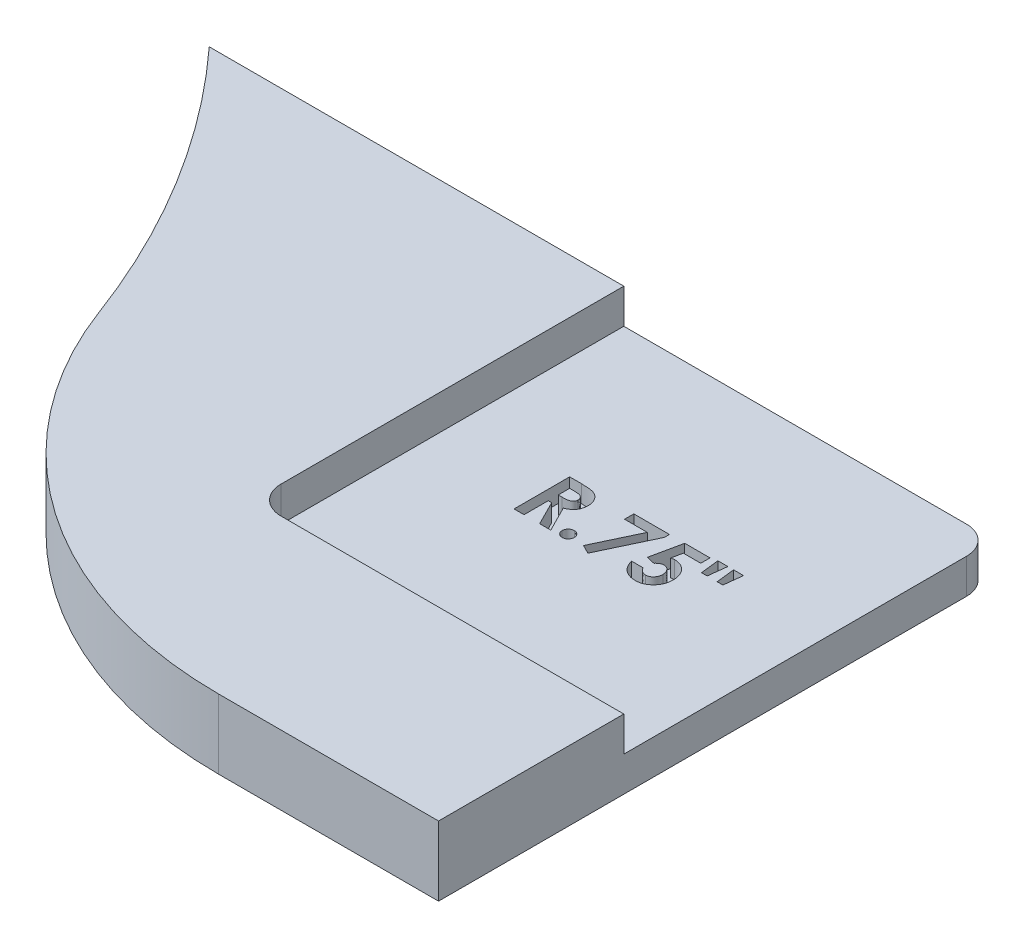
SolidWorks part; units mm, degrees
ref_plane "Front Plane" through (0, 0, 0) normal (0, 0, 1) x (1, 0, 0)
ref_plane "Top Plane" through (0, 0, 0) normal (0, 1, 0) x (1, 0, 0)
ref_plane "Right Plane" through (0, 0, 0) normal (1, 0, 0) x (0, 0, -1)
sketch "Sketch2" plane through (0, 0, 0) normal (0, 1, 0) x (1, 0, 0)
  line L0 (39.9034, 0) -> (66.5271, 0) construction
  line L4 (39.8718, 1.5875) -> (65.2718, 1.5875)
  line L5 (65.2718, 1.5875) -> (65.2718, 26.9875)
  line L6 (65.2718, 26.9875) -> (29.3931, 26.9875)
  arc A0 (39.8718, 1.5875) -> (29.3931, 26.9875) centre (0, 0) ccw
  arc A1 (29.3931, 26.9875) -> (-39.9034, 0) centre (0, 0) ccw construction
  arc A2 (-39.9034, 0) -> (39.9034, 0) centre (0, 0) ccw construction
  arc A3 (39.9034, 0) -> (39.8718, 1.5875) centre (0, 0) ccw construction
  point P6 (45.8249, 5.2638)
  point P7 (37.9479, 12.3384)
  point P10 (43.0639, 5.8161)
extrude "Boss-Extrude1" add sketch "Sketch2" along normal mid plane 3.175
fillet "Fillet1" radius 19.05 1 edges at (39.8718, 0, -1.5875)
sketch "Sketch3" plane through (0, 1.5875, 0) normal (0, 1, 0) x (1, 0, 0)
  line L1 (65.2718, 26.9875) -> (48.3385, 26.9875)
  line L2 (65.2718, 26.9875) -> (65.2718, 10.0542)
  line L3 (65.2718, 10.0542) -> (48.3385, 10.0542)
  line L4 (48.3385, 26.9875) -> (48.3385, 10.0542)
  dimension "D1" = 16.9333
extrude "Cut-Extrude1" cut sketch "Sketch3" against normal blind 1.5875
sketch "Sketch4" plane through (0, 0, 0) normal (0, 1, 0) x (1, 0, 0)
  line L0 (48.3385, 18.5208) -> (65.2718, 18.5208) construction
  line L1 (48.3385, 26.9875) -> (48.3385, 10.0542) construction
  line L2 (65.2718, 10.0542) -> (65.2718, 26.9875) construction
  line L3 (48.3385, 17.2508) -> (65.2718, 17.2508) construction
  text T0 "<b>R.75\"</b>\r\n<b> </b>" font "Century Gothic" height 2.54
  dimension "D1" = 1.27
extrude "Cut-Extrude2" cut sketch "Sketch4" against normal blind 0.7937
fillet "Fillet2" radius 1.27 2 edges at (48.3385, 0.7937, -10.0542) (65.2718, -0.7937, -26.9875)
equation "\"AIRFRAME_OD\"= 3.142in"
equation "\"AIRFRAME_ID\"= 3.00in"
equation "\"FLAT_T\"= 0.125in"
equation "\"NOSE_EXP_L\"= 3.5in"
equation "\"NOSE_SHOULDER_L\"= 5in"
equation "\"MAIN_L\"= 30in"
equation "\"RECO_COUP_L\"= 6in"
equation "\"RECO_SWITCH_L\"= 1.5in"
equation "\"DROGUE_L\"= 14in"
equation "\"ATS_FORE_COUP_L\"= 4in"
equation "\"ATS_AFT_COUP_L\"= 2.5in"
equation "\"LOWER_L\"= 16in"
equation "\"FIN_N\"= 4"
equation "\"CR_AFT_X\"= 0.5in"
equation "\"CR_FORE_X\"= 6in"
equation "\"D1@Sketch2\"=\"AIRFRAME_OD\""
equation "\"D2@Sketch2\"=\"FLAT_T\"/2"
equation "\"D1@Boss-Extrude1\"=\"FLAT_T\""
